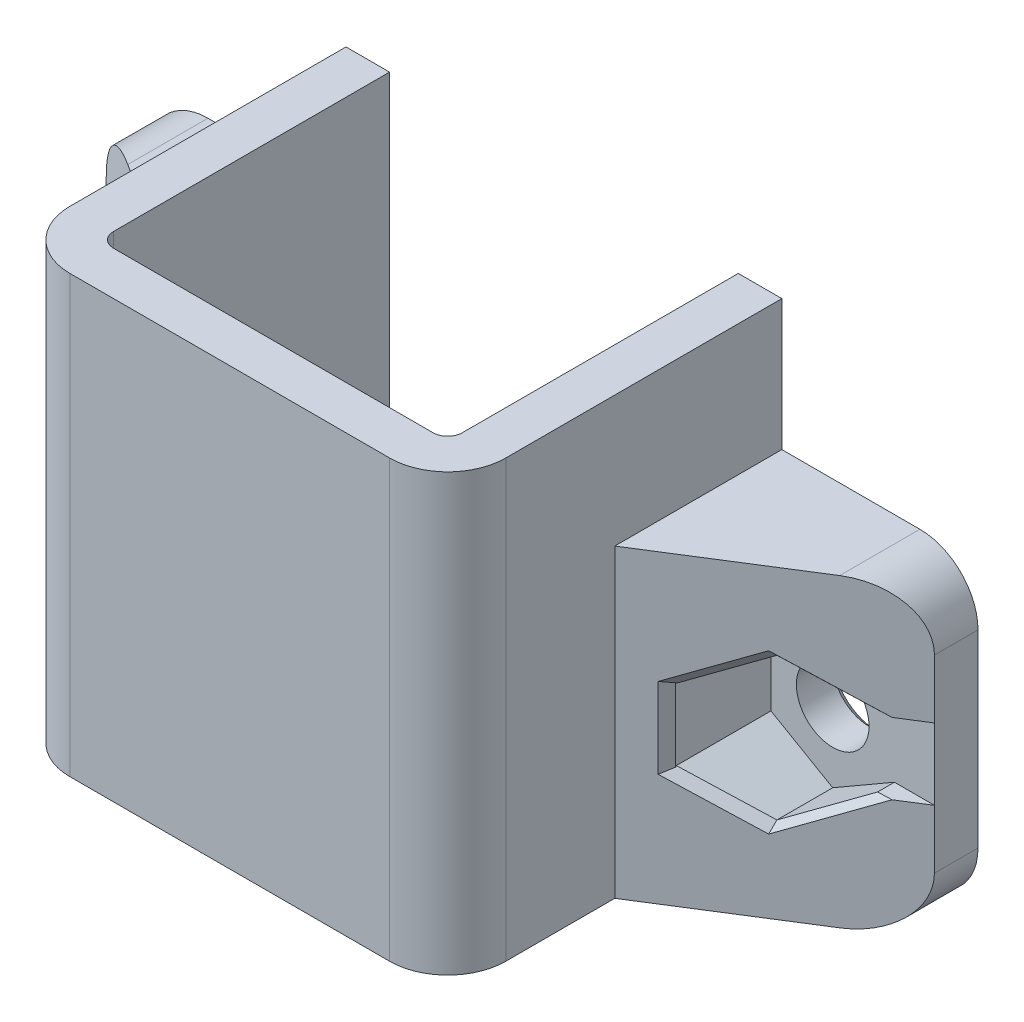
SolidWorks part; units mm, degrees
material "ABS"
ref_plane "Plan de face" through (0, 0, 0) normal (0, 0, 1) x (1, 0, 0)
ref_plane "Plan de dessus" through (0, 0, 0) normal (0, 1, 0) x (1, 0, 0)
ref_plane "Plan de droite" through (0, 0, 0) normal (1, 0, 0) x (0, 0, -1)
sketch "Esquisse1" plane through (0, 0, 0) normal (0, 0, 1) x (1, 0, 0)
  line L1 (-7.5, -7.5) -> (7.5, -7.5)
  line L2 (-7.5, -7.5) -> (-7.5, 7.5)
  line L3 (-7.5, 7.5) -> (7.5, 7.5)
  line L4 (7.5, -7.5) -> (7.5, 7.5)
  line L5 (-7.5, -7.5) -> (7.5, 7.5) construction
  line L6 (-7.5, 7.5) -> (7.5, -7.5) construction
  point P0 (0, 0)
  dimension "D1" = 15
  dimension "D2" = 15
extrude "Boss.-Extru.1" add sketch "Esquisse1" along normal blind 11.5
sketch "Esquisse2" plane through (0, 0, 0) normal (0, 0, -1) x (-1, 0, 0)
  line L0 (7.5, -7.5) -> (-7.5, -7.5) construction
  line L1 (6, 7.5) -> (-6, 7.5)
  line L2 (6, 7.5) -> (6, -7.5)
  line L3 (6, -7.5) -> (-6, -7.5)
  line L4 (-6, 7.5) -> (-6, -7.5)
  line L5 (6, 7.5) -> (-6, -7.5) construction
  line L6 (6, -7.5) -> (-6, 7.5) construction
  point P0 (0, 0)
  dimension "D1" = 12
extrude "Enlèv. mat.-Extru.1" cut sketch "Esquisse2" against normal blind 10
fillet "Congé1" radius 2 2 edges at (7.5, 0, 11.5) (-7.5, 0, 11.5)
sketch "Esquisse3" plane through (0, 0, 10) normal (0, 0, -1) x (-1, 0, 0)
  line L1 (-6, 7.5) -> (-5.5, 7.5)
  line L2 (-6, 7.5) -> (-6, 1.5)
  line L3 (-6, 1.5) -> (-5.5, 1.5)
  line L4 (-5.5, 7.5) -> (-5.5, 1.5)
  line L5 (6, 7.5) -> (5.5, 7.5)
  line L6 (6, 7.5) -> (6, 1.5)
  line L7 (6, 1.5) -> (5.5, 1.5)
  line L8 (5.5, 7.5) -> (5.5, 1.5)
  dimension "D1" = 6
  dimension "D2" = 6
  dimension "D3" = 0.5
  dimension "D4" = 0.5
extrude "Boss.-Extru.2" add sketch "Esquisse3" along normal blind 0.5
sketch "Esquisse4" plane through (0, 1.5, 0) normal (0, -1, 0) x (1, 0, 0)
  line L0 (-6, 9.5) -> (-5.5, 9.5)
  line L1 (6, 9.5) -> (5.5, 9.5) construction
  line L2 (6, 9.5) -> (6, 10) construction
  line L3 (6, 10) -> (5.5, 10) construction
  line L4 (5.5, 9.5) -> (5.5, 10) construction
  line L5 (-5.5, 9.5) -> (-6, 9.5) construction
  line L6 (-5.5, 9.5) -> (-5.5, 10) construction
  line L7 (-5.5, 10) -> (-6, 10) construction
  line L8 (-6, 9.5) -> (-6, 10) construction
  line L9 (-5.5, 9.5) -> (-5.5, 10)
  line L10 (6, 9.5) -> (5.5, 9.5)
  line L11 (5.5, 9.5) -> (5.5, 10)
  arc A0 (5.5, 10) -> (6, 9.5) centre (5.5, 9.5) cw
  arc A1 (-5.5, 10) -> (-6, 9.5) centre (-5.5, 9.5) ccw
extrude "Enlèv. mat.-Extru.2" cut sketch "Esquisse4" against normal up to surface (6 mm away) up to face at (0, 7.5, 7.202)
sketch "Esquisse5" plane through (0, 0, 10) normal (0, 0, -1) x (-1, 0, 0)
  line L0 (-6, 1.5) -> (-6, -7.5) construction
  line L1 (-6, -6.5) -> (-2.5, -6.5)
  line L2 (-6, -6.5) -> (-6, -2.5)
  line L3 (-6, -2.5) -> (-2.5, -2.5)
  line L4 (-2.5, -6.5) -> (-2.5, -2.5)
  line L6 (-6, -1.5) -> (-2.5, -1.5)
  line L7 (-6, -1.5) -> (-6, 0.5)
  line L8 (-6, 0.5) -> (-2.5, 0.5)
  line L9 (-2.5, -1.5) -> (-2.5, 0.5)
  dimension "D1" = 1
  dimension "D2" = 1
  dimension "D3" = 2
  dimension "D4" = 4
  dimension "D5" = 3.5
  dimension "D6" = 3.5
extrude "Boss.-Extru.3" add sketch "Esquisse5" along normal blind 0.4
sketch "Esquisse6" plane through (0, 0, 9.6) normal (0, 0, -1) x (-1, 0, 0)
  line L0 (-2.5, -2.5) -> (-6, -2.5) construction
  line L1 (-6, -6.5) -> (-5.6, -6.5)
  line L2 (-6, -6.5) -> (-6, -2.5)
  line L3 (-6, -2.5) -> (-5.6, -2.5)
  line L4 (-5.6, -6.5) -> (-5.6, -2.5)
  line L5 (-2.5, 0.5) -> (-6, 0.5) construction
  line L6 (-6, -1.5) -> (-5.6, -1.5)
  line L7 (-6, -1.5) -> (-6, 0.5)
  line L8 (-6, 0.5) -> (-5.6, 0.5)
  line L9 (-5.6, -1.5) -> (-5.6, 0.5)
  dimension "D1" = 0.4
  dimension "D2" = 0.4
extrude "Boss.-Extru.4" add sketch "Esquisse6" along normal blind 3.1
fillet "Congé3" radius 0.5 2 edges at (5.6, -0.5, 9.6) (5.6, -4.5, 9.6)
sketch "Esquisse7" plane through (0, 0, 0) normal (0, 0, -1) x (-1, 0, 0)
  line L1 (-7.5, -7.5) -> (-14.25, -7.5)
  line L2 (-7.5, -7.5) -> (-7.5, 3)
  line L3 (-7.5, 3) -> (-14.25, 3)
  line L4 (-14.25, -7.5) -> (-14.25, 3)
  line L5 (7.5, -7.5) -> (14.25, -7.5)
  line L6 (7.5, -7.5) -> (7.5, 3)
  line L7 (7.5, 3) -> (14.25, 3)
  line L8 (14.25, -7.5) -> (14.25, 3)
  dimension "D1" = 6.75
  dimension "D2" = 6.75
  dimension "D3" = 10.5
  dimension "D4" = 10.5
extrude "Boss.-Extru.5" add sketch "Esquisse7" against normal blind 1.5
sketch "Esquisse12" plane through (0, 0, 0) normal (0, 0, -1) x (-1, 0, 0)
  line L0 (14.25, -2.25) -> (-14.25, -2.25) construction
  line L1 (14.25, -7.5) -> (14.25, 3) construction
  line L2 (-14.25, 3) -> (-14.25, -7.5) construction
  circle A0 centre (10.75, -2.25) radius 1.25
  circle A1 centre (-10.75, -2.25) radius 1.25
  point P10 (0, -2.25)
  dimension "D2" = 2.5
  dimension "D3" = 2.5
  dimension "D1" = 21.5
  dimension "D4" = 10.75
extrude "Enlèv. mat.-Extru.6" cut sketch "Esquisse12" against normal up to surface (1.5 mm away) up to face at (-10.875, -2.25, 1.5)
sketch "Esquisse13" plane through (0, 0, 1.5) normal (0, 0, 1) x (1, 0, 0)
  line L0 (14.25, 3) -> (14.25, -7.5) construction
  line L1 (-10.75, -4.7037) -> (-8.625, -3.4769) construction
  line L2 (-8.625, -3.4769) -> (-8.625, -1.0231) construction
  line L3 (-8.625, -1.0231) -> (-10.75, 0.2037) construction
  line L4 (-10.75, 0.2037) -> (-13.107, -1.1571) construction
  line L6 (-13.107, -3.3429) -> (-10.75, -4.7037) construction
  line L7 (10.75, 0.2037) -> (8.625, -1.0231) construction
  line L8 (8.625, -1.0231) -> (8.625, -3.4769) construction
  line L9 (8.625, -3.4769) -> (10.75, -4.7037) construction
  line L10 (10.75, -4.7037) -> (12.875, -3.4769) construction
  line L12 (12.875, -1.0231) -> (10.75, 0.2037) construction
  line L13 (12.875, -3.4769) -> (14.25, -3.4769) construction
  line L15 (12.875, -1.0231) -> (14.25, -1.0231) construction
  line L16 (14.25, -3.4769) -> (14.25, -1.0231) construction
  line L17 (12.875, -3.7448) -> (12.875, -1.1467) [skipped]
  line L18 (-14.25, -7.5) -> (-14.25, 3) construction
  line L19 (-13.107, -1.1571) -> (-14.25, -1.1571) construction
  line L21 (-13.107, -3.3429) -> (-14.25, -3.3429) construction
  line L22 (-14.25, -1.1571) -> (-14.25, -3.3429) construction
  line L23 (-12.875, -0.7552) -> (-12.875, -3.3533) [skipped]
  line L24 (-7.5, 3) -> (-7.5, -7.5)
  line L25 (-7.5, -7.5) -> (-14.25, -7.5)
  line L26 (-14.25, -7.5) -> (-14.25, -3.3429)
  line L27 (-14.25, -3.3429) -> (-13.107, -3.3429)
  line L28 (-13.107, -3.3429) -> (-10.75, -4.7037)
  line L29 (-10.75, -4.7037) -> (-8.625, -3.4769)
  line L30 (-8.625, -3.4769) -> (-8.625, -1.0231)
  line L31 (-8.625, -1.0231) -> (-10.75, 0.2037)
  line L32 (-10.75, 0.2037) -> (-13.107, -1.1571)
  line L33 (-13.107, -1.1571) -> (-14.25, -1.1571)
  line L34 (-14.25, -1.1571) -> (-14.25, 3)
  line L35 (-14.25, 3) -> (-7.5, 3)
  line L36 (7.5, -7.5) -> (7.5, 3)
  line L37 (7.5, 3) -> (14.25, 3)
  line L38 (14.25, 3) -> (14.25, -1.0231)
  line L39 (14.25, -1.0231) -> (12.875, -1.0231)
  line L40 (12.875, -1.0231) -> (10.75, 0.2037)
  line L41 (10.75, 0.2037) -> (8.625, -1.0231)
  line L42 (8.625, -1.0231) -> (8.625, -3.4769)
  line L43 (8.625, -3.4769) -> (10.75, -4.7037)
  line L44 (10.75, -4.7037) -> (12.875, -3.4769)
  line L45 (12.875, -3.4769) -> (14.25, -3.4769)
  line L46 (14.25, -3.4769) -> (14.25, -7.5)
  line L47 (14.25, -7.5) -> (7.5, -7.5)
  line L48 (12.875, -3.4769) -> (12.875, -1.0231) construction
  line L49 (-13.107, -1.1571) -> (-13.107, -3.3429) construction
  circle A0 centre (-10.75, -2.25) radius 2.125 construction
  circle A1 centre (10.75, -2.25) radius 2.125 construction
  dimension "D1" = 4.25
  dimension "D2" = 4.25
extrude "Boss.-Extru.6" add sketch "Esquisse13" along normal blind 4.25
sketch "Esquisse14" plane through (0, -7.5, 0) normal (0, -1, 0) x (1, 0, 0)
  line L0 (-7.5, 5.75) -> (-14.25, 1.5)
  line L1 (-14.25, 5.75) -> (-14.25, 0) construction
  line L2 (-14.25, 1.5) -> (-14.25, 5.75)
  line L3 (-14.25, 5.75) -> (-7.5, 5.75)
  line L4 (7.5, 5.75) -> (14.25, 1.5)
  line L5 (14.25, 5.75) -> (14.25, 0) construction
  line L6 (14.25, 1.5) -> (14.25, 5.75)
  line L7 (14.25, 5.75) -> (7.5, 5.75)
  dimension "D1" = 4.25
  dimension "D2" = 4.25
extrude "Enlèv. mat.-Extru.7" cut sketch "Esquisse14" against normal up to surface (10.5 mm away) up to face at (10.875, 3, 2.875)
fillet "Congé5" radius 2 4 edges at (14.25, 3, 0.75) (14.25, -7.5, 0.75) (-14.25, 3, 0.75) (-14.25, -7.5, 0.75)
chamfer "Chanfrein2" distance 0.25 10 edges at (-11.9285, -0.4767, 2.9617) (-11.9285, -4.0233, 2.9617) (-9.6875, -4.0903, 4.3727) (-8.625, -2.25, 5.0417) (-9.6875, -0.4097, 4.3727) (11.8125, -0.4097, 3.0347) (9.6875, -0.4097, 4.3727) (8.625, -2.25, 5.0417) (9.6875, -4.0903, 4.3727) (11.8125, -4.0903, 3.0347)
chamfer "Chanfrein3" distance 0.25 2 edges at (9.5, -2.25, 0) (-12, -2.25, 0)
chamfer "Chanfrein4" distance 0.25 12 edges at (5.6, 0.5, 7.8) (5.4536, 0.5, 9.4536) (3.8, 0.5, 9.6) (3.8, -1.5, 9.6) (5.4536, -1.5, 9.4536) (5.6, -1.5, 7.8) (5.6, -2.5, 7.8) (5.4536, -2.5, 9.4536) (3.8, -2.5, 9.6) (3.8, -6.5, 9.6) (5.4536, -6.5, 9.4536) (5.6, -6.5, 7.8)
